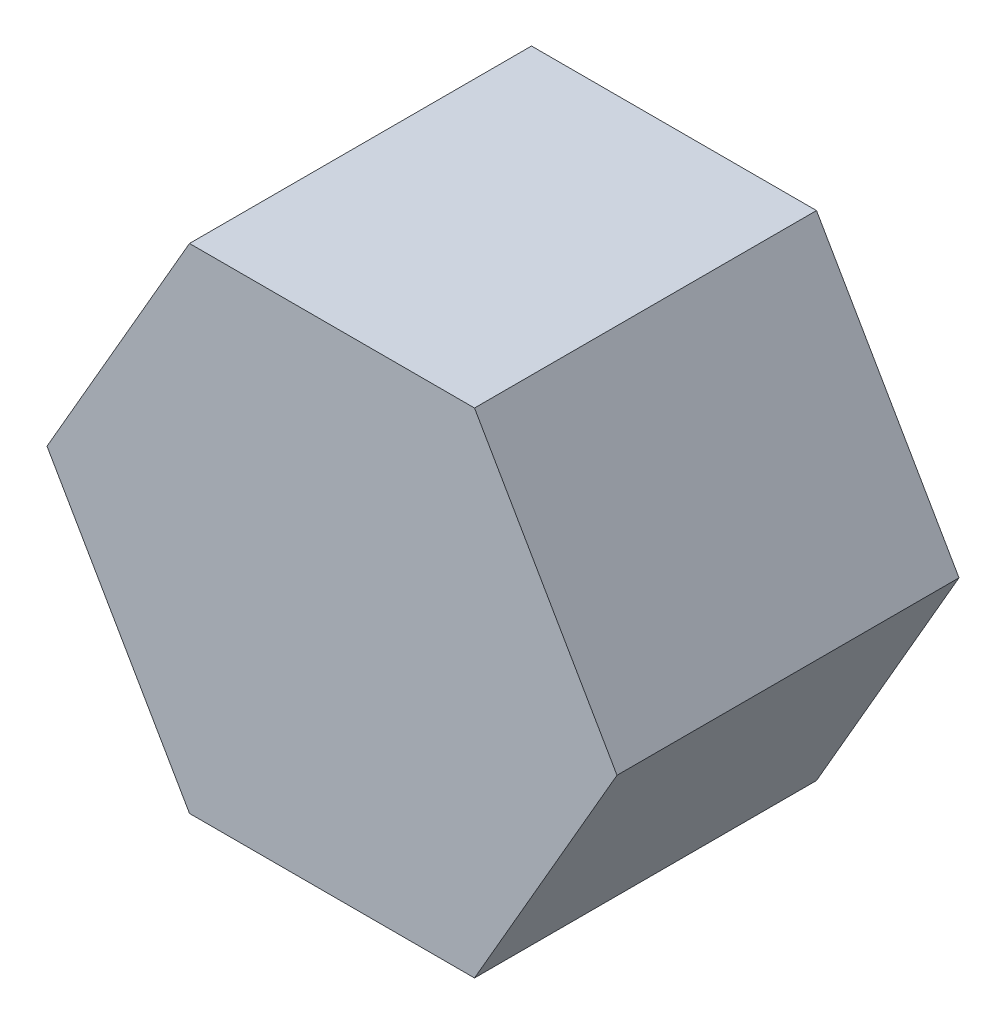
SolidWorks part; units mm, degrees
ref_plane "Piano frontale" through (0, 0, 0) normal (0, 0, 1) x (1, 0, 0)
ref_plane "Piano superiore" through (0, 0, 0) normal (0, 1, 0) x (1, 0, 0)
ref_plane "Piano destro" through (0, 0, 0) normal (1, 0, 0) x (0, 0, -1)
sketch "Schizzo1" plane through (0, 0, 0) normal (0, 0, 1) x (1, 0, 0)
  line L1 (-12.5, -21.6506) -> (12.5, -21.6506)
  line L2 (12.5, -21.6506) -> (25, 0)
  line L3 (25, 0) -> (12.5, 21.6506)
  line L4 (12.5, 21.6506) -> (-12.5, 21.6506)
  line L5 (-12.5, 21.6506) -> (-25, 0)
  line L6 (-25, 0) -> (-12.5, -21.6506)
  circle A0 centre (0, 0) radius 25 construction
  dimension "D1" = 50
extrude "Estrusione-Estrusione1" add sketch "Schizzo1" along normal blind 30
